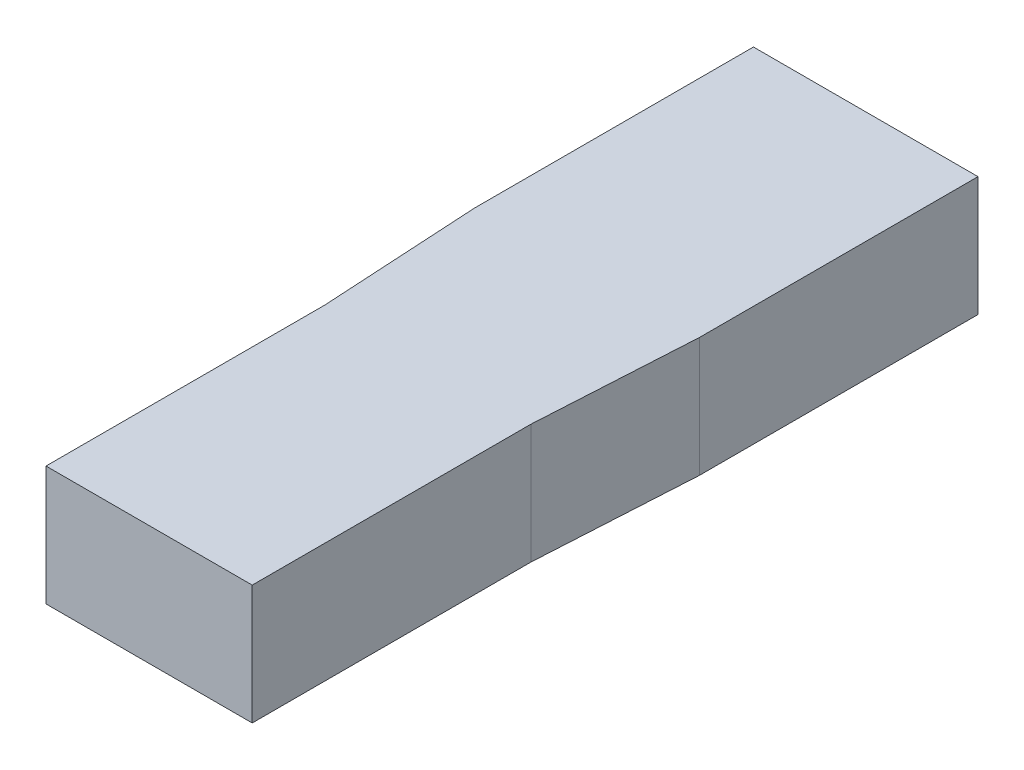
SolidWorks part; units mm, degrees
ref_plane "Front Plane" through (0, 0, 0) normal (0, 0, 1) x (1, 0, 0)
ref_plane "Top Plane" through (0, 0, 0) normal (0, 1, 0) x (1, 0, 0)
ref_plane "Right Plane" through (0, 0, 0) normal (1, 0, 0) x (0, 0, -1)
sketch "Sketch1" plane through (0, 0, 0) normal (0, 1, 0) x (1, 0, 0)
  line L1 (-2.82, -9) -> (2.82, -9)
  line L2 (-2.82, -9) -> (-2.82, 9)
  line L3 (-2.82, 9) -> (2.82, 9)
  line L4 (2.82, -9) -> (2.82, 9)
  line L5 (-2.82, -9) -> (2.82, 9) construction
  line L6 (-2.82, 9) -> (2.82, -9) construction
  point P0 (0, 0)
  dimension "D1" = 5.64
  dimension "D2" = 18
extrude "Boss-Extrude1" add sketch "Sketch1" along normal blind 3
sketch "Sketch2" plane through (0, 3, 0) normal (0, 1, 0) x (1, 0, 0)
  line L0 (-2.59, -9) -> (-2.59, -2)
  line L1 (-2.82, -9) -> (2.82, -9) construction
  line L2 (-2.59, -2) -> (-2.82, 2)
  line L3 (-2.82, 9) -> (-2.82, -9) construction
  line L4 (-2.82, 2) -> (-2.82, -9)
  line L5 (-2.82, -9) -> (-2.59, -9)
  line L6 (-2.59, -9) -> (-5.2498, -15.2389)
  dimension "D1" = 7
  dimension "D2" = 4
  dimension "D3" = 0.23
extrude "Cut-Extrude1" cut sketch "Sketch2" against normal through all both and the other way through all contours L0 L2 L4 L5
mirror "Mirror1" about plane through (0, 0, 0) normal (1, 0, 0) of "Cut-Extrude1"
